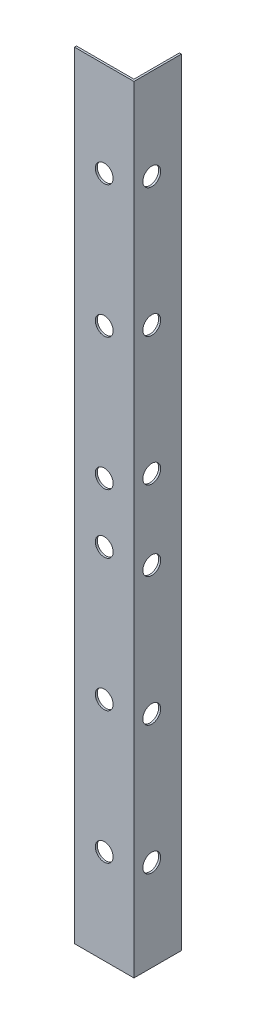
SolidWorks part; units mm, degrees
material "6061-T6 (SS)"
ref_plane "Alzado" through (0, 0, 0) normal (0, 0, 1) x (1, 0, 0)
ref_plane "Planta" through (0, 0, 0) normal (0, 1, 0) x (1, 0, 0)
ref_plane "Vista lateral" through (0, 0, 0) normal (1, 0, 0) x (0, 0, -1)
sketch "Sketch1" plane through (0, 0, 0) normal (0, 1, 0) x (1, 0, 0)
  line L0 (0, 0) -> (15, 0)
  line L1 (15, 0) -> (15, 12)
  line L2 (15, 12) -> (14.5, 12)
  line L3 (14.5, 12) -> (14.5, 0.5)
  line L4 (14.5, 0.5) -> (0, 0.5)
  line L5 (0, 0.5) -> (0, 0)
  dimension "D1" = 15
  dimension "D2" = 12
  dimension "D3" = 0.5
  dimension "D4" = 0.5
extrude "Boss-Extrude1" add sketch "Sketch1" along normal blind 196
sketch "Sketch4" plane through (0, 0, 0) normal (0, 0, 1) x (1, 0, 0)
  line L0 (15, 196) -> (15, 0) construction
  line L1 (0, 196) -> (15, 196)
  line L2 (0, 196) -> (0, 193)
  line L3 (0, 193) -> (15, 193)
  line L4 (15, 196) -> (15, 193)
  line L6 (0, 0) -> (15, 0)
  line L7 (0, 0) -> (0, 3)
  line L8 (0, 3) -> (15, 3)
  line L9 (15, 0) -> (15, 3)
  dimension "D1" = 3
  dimension "D2" = 3
extrude "Cut-Extrude3" [suppressed] cut sketch "Sketch4" against normal up to next
sketch "Sketch5" plane through (15, 0, 0) normal (1, 0, 0) x (0, 0, -1)
  circle A0 centre (4.5, 23) radius 2.25
  circle A1 centre (4.5, 55.5) radius 2.25
  circle A2 centre (4.5, 88) radius 2.25
  circle A3 centre (4.5, 108) radius 2.25
  circle A4 centre (4.5, 140.5) radius 2.25
  circle A5 centre (4.5, 173) radius 2.25
  point P18 (0, 0)
  point P19 (0, 0)
  point P20 (0, 0)
  point P21 (0, 0)
  point P22 (0, 0)
  point P23 (0, 0)
  dimension "D1" = 4.5
extrude "Cut-Extrude4" cut sketch "Sketch5" against normal up to next
sketch "Sketch6" plane through (0, 0, 0) normal (0, 0, 1) x (1, 0, 0)
  circle A0 centre (7.5, 23.8333) radius 2.25
  circle A1 centre (7.5, 57.1667) radius 2.25
  circle A2 centre (7.5, 90.5) radius 2.25
  circle A3 centre (7.5, 105.5) radius 2.25
  circle A4 centre (7.5, 138.8333) radius 2.25
  circle A5 centre (7.5, 172.1667) radius 2.25
  dimension "D1" = 4.5
extrude "Cut-Extrude5" cut sketch "Sketch6" against normal up to next
